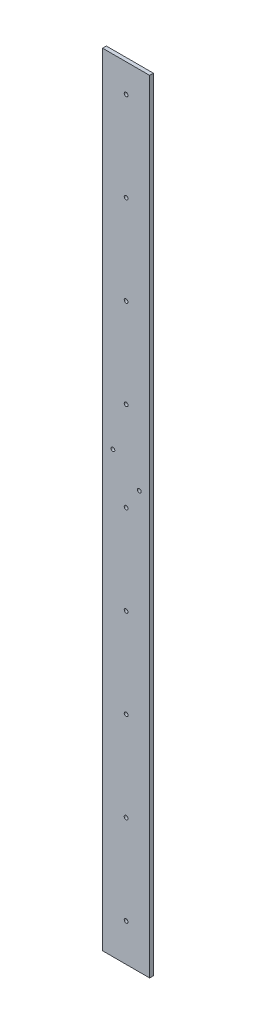
SolidWorks part; units mm, degrees
ref_plane "Front Plane" through (0, 0, 0) normal (0, 0, 1) x (1, 0, 0)
ref_plane "Top Plane" through (0, 0, 0) normal (0, 1, 0) x (1, 0, 0)
ref_plane "Right Plane" through (0, 0, 0) normal (1, 0, 0) x (0, 0, -1)
sketch "Sketch2" plane through (0, 0, 0) normal (0, 0, 1) x (1, 0, 0)
  line L0 (-24.628, -449.721) -> (25.372, -449.721)
  line L1 (25.372, -449.721) -> (25.372, 450.279)
  line L2 (25.372, 450.279) -> (-24.628, 450.279)
  line L3 (-24.628, 450.279) -> (-24.628, -449.721)
  dimension "D1" = 900
extrude "Boss-Extrude1" add sketch "Sketch2" along normal blind 4
sketch "Sketch3" plane through (0, 0, 4) normal (0, 0, 1) x (1, 0, 0)
  line L0 (25.372, -449.721) -> (25.372, 450.279) construction
  line L1 (25.372, -379.721) -> (-24.628, -379.721)
  line L2 (25.372, -379.721) -> (25.372, -449.721)
  line L3 (25.372, -449.721) -> (-24.628, -449.721)
  line L4 (-24.628, -379.721) -> (-24.628, -449.721)
  line L5 (-24.628, -379.721) -> (25.372, -379.721) construction
extrude "Cut-Extrude1" cut sketch "Sketch3" against normal up to next
sketch "Sketch4" plane through (0, 0, 0) normal (0, 0, -1) x (-1, 0, 0)
  circle A0 centre (13.628, 86.9275) radius 2
  circle A1 centre (12.128, 485.279) radius 2
  circle A2 centre (12.128, 485.279) radius 2
  circle A3 centre (-0.372, 500.279) radius 2
  circle A4 centre (-0.372, 500.279) radius 2
  circle A5 centre (-0.372, 470.279) radius 2
  circle A6 centre (-0.372, 470.279) radius 2
  circle A7 centre (-0.372, -244.721) radius 2
  circle A8 centre (-0.372, -244.721) radius 2
  circle A9 centre (-0.372, -149.721) radius 2
  circle A10 centre (-0.372, -149.721) radius 2
  circle A11 centre (-0.372, -54.721) radius 2
  circle A12 centre (-0.372, -54.721) radius 2
  circle A13 centre (-0.372, 40.279) radius 2
  circle A14 centre (-0.372, 40.279) radius 2
  circle A15 centre (-0.372, 135.279) radius 2
  circle A16 centre (-0.372, 135.279) radius 2
  circle A17 centre (-0.372, 230.279) radius 2
  circle A18 centre (-0.372, 230.279) radius 2
  circle A19 centre (-0.372, 325.279) radius 2
  circle A20 centre (-0.372, 325.279) radius 2
  circle A21 centre (-0.372, 420.279) radius 2
  circle A22 centre (-0.372, 420.279) radius 2
  circle A23 centre (-0.372, -339.721) radius 2
  circle A24 centre (-0.372, -339.721) radius 2
  circle A25 centre (-14.372, 62.7991) radius 2
  dimension "D1" = 0
  dimension "D2" = 0
  dimension "D3" = 0
  dimension "D4" = 0
  dimension "D5" = 0
  dimension "D6" = 0
  dimension "D7" = 0
  dimension "D8" = 0
  dimension "D9" = 0
  dimension "D10" = 0
  dimension "D11" = 0
  dimension "D12" = 0
extrude "Cut-Extrude4" cut sketch "Sketch4" against normal through all
